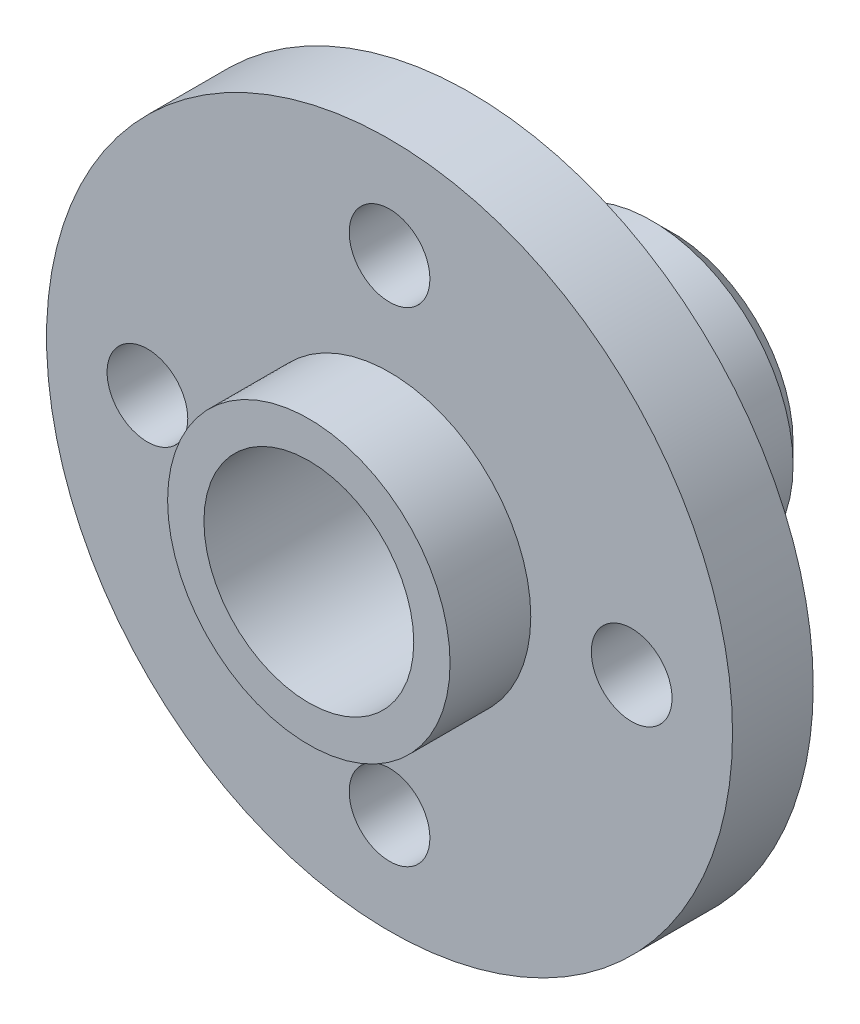
SolidWorks part; units mm, degrees
material "ABS"
ref_plane "Спереди" through (0, 0, 0) normal (0, 0, 1) x (1, 0, 0)
ref_plane "Сверху" through (0, 0, 0) normal (0, 1, 0) x (1, 0, 0)
ref_plane "Справа" through (0, 0, 0) normal (1, 0, 0) x (0, 0, -1)
sketch "Эскиз2" plane through (0, 0, 0) normal (0, 0, 1) x (1, 0, 0)
  line L0 (0, 0) -> (-8.5, 0) construction
  circle A0 centre (0, 0) radius 2.6
  circle A1 centre (0, 0) radius 8.5
  circle A2 centre (-6, 0) radius 1
  circle A3 centre (0, 6) radius 1
  circle A4 centre (6, 0) radius 1
  circle A5 centre (0, -6) radius 1
  point P16 (0, 0)
  dimension "D1" = 17
  dimension "D2" = 5.2
  dimension "D3" = 2
  dimension "D4" = 6
  dimension "D5" = 4
extrude "Бобышка-Вытянуть1" add sketch "Эскиз2" along normal blind 2
sketch "Эскиз3" plane through (0, 0, 2) normal (0, 0, 1) x (1, 0, 0)
  circle A0 centre (0, 0) radius 2.6
  circle A1 centre (0, 0) radius 3.5
  dimension "D1" = 7
  dimension "D2" = 5.2
extrude "Бобышка-Вытянуть2" add sketch "Эскиз3" along normal blind 2
sketch "Эскиз4" plane through (0, 0, 0) normal (0, 0, -1) x (-1, 0, 0)
  circle A0 centre (0, 0) radius 3.5
  circle A1 centre (0, 0) radius 2.6
  dimension "D1" = 7
extrude "Бобышка-Вытянуть3" add sketch "Эскиз4" along normal blind 5
chamfer "Фаска1" distance 0.5 angle 45 1 edges at (-3.5, 0, -5)
